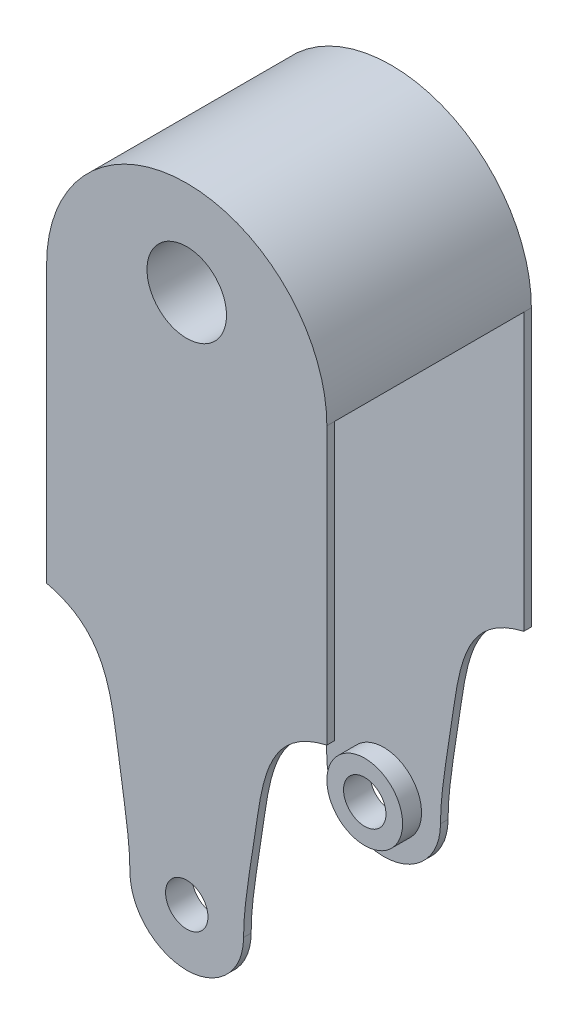
SolidWorks part; units mm, degrees
ref_plane "Alzado" through (0, 0, 0) normal (0, 0, 1) x (1, 0, 0)
ref_plane "Planta" through (0, 0, 0) normal (0, 1, 0) x (1, 0, 0)
ref_plane "Vista lateral" through (0, 0, 0) normal (1, 0, 0) x (0, 0, -1)
sketch "Croquis1" plane through (0, 0, 0) normal (0, 0, 1) x (1, 0, 0)
  line L2 (74, 180) -> (37, 180) construction
  line L3 (0, 143) -> (0, 70)
  line L4 (74, 143) -> (74, 180) construction
  line L6 (37, 0) -> (37, 15)
  line L7 (37, 15) -> (37, 40) construction
  line L8 (37, 40) -> (19, 40) construction
  line L9 (74, 143) -> (74, 70)
  line L10 (74, 70) -> (74, 0) construction
  line L11 (37, 180) -> (37, 155) construction
  arc A0 (74, 143) -> (0, 143) centre (37, 143) ccw
  circle A2 centre (37, 15) radius 5.6
  arc A3 (22, 15) -> (52, 15) centre (37, 15) ccw
  circle A4 centre (37, 155) radius 10.5
  spline S0 degree 3 poles (52, 15) (52, 22.318) (56.2223, 44.5245) (58.0965, 66.3006) (74, 70) knots 0 0 0 0 0.399675 1 1 1 1
  spline S1 degree 3 poles (22, 15) (22, 22.318) (17.7777, 44.5245) (15.9035, 66.3006) (0, 70) knots 0 0 0 0 0.399675 1 1 1 1
  dimension "D3" = 21
  dimension "D4" = 11.2
  dimension "D9" = 15
  dimension "D1" = 180
  dimension "D2" = 74
  dimension "D5" = 15
  dimension "D6" = 25
  dimension "D7" = 18
  dimension "D8" = 20
  dimension "D11" = 25
extrude "Saliente-Extruir1" add sketch "Croquis1" along normal blind 54
sketch "Croquis2" plane through (74, 0, 0) normal (1, 0, 0) x (0, 0, -1)
  line L0 (-54, 70) -> (-52, 70) construction
  line L1 (-54, 70) -> (0, 70) construction
  line L2 (-52, 70) -> (-2, 70)
  line L3 (-2, 70) -> (0, 70) construction
  line L4 (-52, 70) -> (-52, 20.6)
  line L9 (-52, 20.6) -> (-49, 20.6)
  line L10 (-49, 20.6) -> (-49, 9.4)
  line L11 (-52, 9.4) -> (-49, 9.4)
  line L12 (-52, 9.4) -> (-52, 0)
  line L17 (-2, 9.4) -> (-2, 0)
  line L18 (-2, 9.4) -> (-5, 9.4)
  line L19 (-5, 20.6) -> (-5, 9.4)
  line L20 (-2, 20.6) -> (-5, 20.6)
  line L21 (-2, 70) -> (-2, 20.6)
  line L22 (0, 70) -> (-2, 70) construction
  line L27 (-52, 0) -> (-2, 0)
  point P16 (-49, 15)
  point P31 (-5, 15)
  point P32 (-50.5, 9.4)
  dimension "D1" = 11.2
  dimension "D4" = 3
sketch "Croquis6" plane through (0, 0, 0) normal (-1, 0, 0) x (0, 0, 1)
  line L0 (0, 70) -> (0, 0)
  line L1 (0, 0) -> (54, 0)
  line L2 (54, 0) -> (54, 70)
  line L3 (54, 70) -> (0, 70)
extrude "Saliente-Extruir3" add sketch "Croquis6" against normal blind 74
sketch "Croquis7" plane through (74, 0, 0) normal (1, 0, 0) x (0, 0, -1)
  line L0 (-52, 0) -> (-2, 0)
  line L1 (-2, 0) -> (-2, 9.4)
  line L2 (-2, 9.4) -> (-5, 9.4)
  line L3 (-5, 9.4) -> (-5, 20.6)
  line L4 (-5, 20.6) -> (-2, 20.6)
  line L5 (-2, 20.6) -> (-2, 70)
  line L6 (-2, 70) -> (-52, 70)
  line L7 (-52, 70) -> (-52, 20.6)
  line L8 (-52, 20.6) -> (-49, 20.6)
  line L9 (-49, 20.6) -> (-49, 9.4)
  line L10 (-49, 9.4) -> (-52, 9.4)
  line L11 (-52, 9.4) -> (-52, 0)
extrude "Cortar-Extruir13" cut sketch "Croquis7" against normal blind 74
sketch "Croquis8" plane through (0, 0, 0) normal (0, 0, -1) x (-1, 0, 0)
  line L0 (-74, 70) -> (-74, 0)
  line L1 (-74, 0) -> (-37, 0)
  line L2 (-37, 0) -> (0, 0)
  line L3 (0, 0) -> (0, 70)
  circle A0 centre (-37, 15) radius 5.6
  arc A1 (-52, 15) -> (-22, 15) centre (-37, 15) ccw
  spline S0 degree 3 poles (-74, 70) (-58.0965, 66.3006) (-56.2223, 44.5245) (-52, 22.318) (-52, 15) knots 0 0 0 0 0.600325 1 1 1 1
  spline S1 degree 3 poles (-22, 15) (-22, 22.318) (-17.7777, 44.5245) (-15.9035, 66.3006) (0, 70) knots 0 0 0 0 0.399675 1 1 1 1
  line M1 (-74, 0) -> (0, 0)
  line M2 (0, 0) -> (0, 143)
  line M4 (-74, 143) -> (-74, 0)
extrude "Cortar-Extruir14" cut sketch "Croquis8" against normal blind 74 contours S0 A1 M4 M1 | S1 A1 M1 M2
sketch "Croquis9" plane through (74, 0, 0) normal (1, 0, 0) x (0, 0, -1)
  line L0 (-49, 20.6) -> (-52, 20.6)
  line L1 (-52, 20.6) -> (-52, 9.4)
  line L2 (-52, 9.4) -> (-49, 9.4)
  line L3 (-49, 9.4) -> (-49, 20.6)
  line L4 (-2, 20.6) -> (-5.1988, 20.6)
  line L5 (-5.1988, 20.6) -> (-5, 9.4)
  line L6 (-5, 9.4) -> (-2, 9.4)
  line L7 (-2, 20.6) -> (-2, 9.4)
extrude "Cortar-Extruir15" cut sketch "Croquis9" against normal blind 74
sketch "Croquis10" plane through (0, 0, 0) normal (0, 0, -1) x (-1, 0, 0)
  circle A0 centre (-37, 15) radius 5.6
extrude "Cortar-Extruir16" cut sketch "Croquis10" against normal blind 74
sketch "Croquis11" plane through (0, 0, 52) normal (0, 0, -1) x (-1, 0, 0)
  circle A0 centre (-37, 15) radius 10
  circle A1 centre (-37, 15) radius 5.6
  dimension "D1" = 20
extrude "Saliente-Extruir4" add sketch "Croquis11" along normal blind 5
sketch "Croquis12" plane through (0, 0, 2) normal (0, 0, 1) x (1, 0, 0)
  circle A0 centre (37, 15) radius 5.6
  circle A1 centre (37, 15) radius 10
  dimension "D1" = 20
extrude "Saliente-Extruir5" add sketch "Croquis12" along normal blind 5
sketch "Croquis13" plane through (0, 0, 0) normal (-1, 0, 0) x (0, 0, 1)
  line L0 (2, 70) -> (2, 143)
  line L1 (54, 143) -> (0, 143) construction
  line L2 (2, 143) -> (52, 143)
  line L3 (52, 143) -> (52, 70)
  line L4 (52, 70) -> (2, 70)
extrude "Cortar-Extruir17" cut sketch "Croquis13" against normal blind 74
